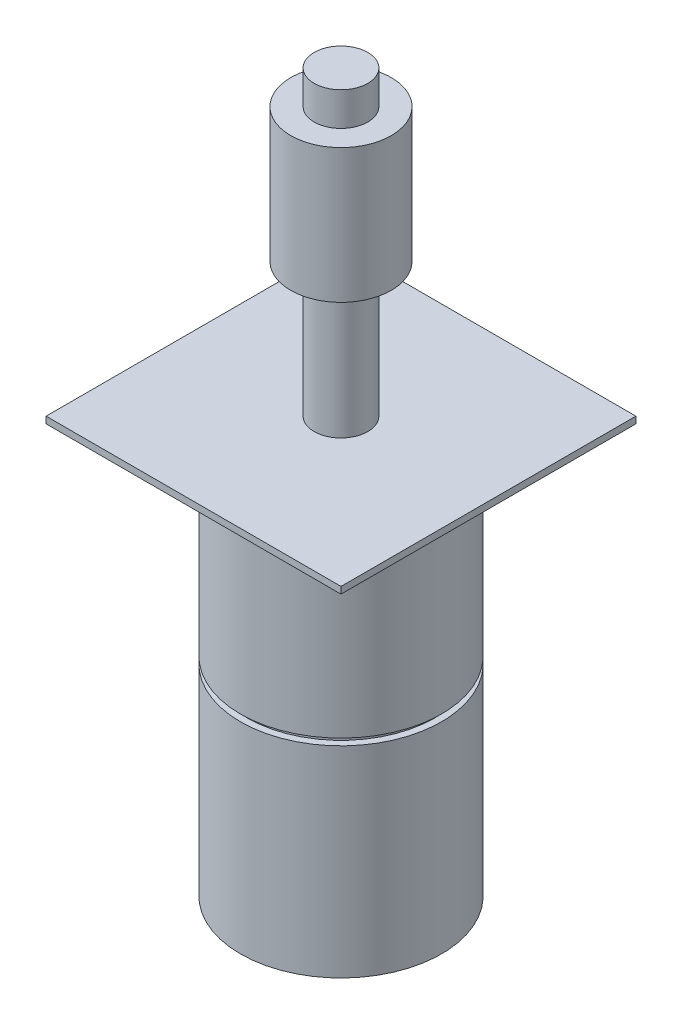
SolidWorks part; units mm, degrees
ref_plane "Front Plane" through (0, 0, 0) normal (0, 0, 1) x (1, 0, 0)
ref_plane "Top Plane" through (0, 0, 0) normal (0, 1, 0) x (1, 0, 0)
ref_plane "Right Plane" through (0, 0, 0) normal (1, 0, 0) x (0, 0, -1)
sketch "Sketch1" plane through (0, 0, 0) normal (0, 1, 0) x (1, 0, 0)
  circle A0 centre (0, 0) radius 15
extrude "Boss-Extrude1" add sketch "Sketch1" along normal blind 30
ref_plane "Plane1" through (0, 30, 0) normal (0, 1, 0) x (1, 0, 0)
sketch "Sketch2" plane through (0, 30, 0) normal (0, 1, 0) x (1, 0, 0)
  line L1 (-22, 22) -> (22, 22)
  line L2 (-22, 22) -> (-22, -22)
  line L3 (-22, -22) -> (22, -22)
  line L4 (22, 22) -> (22, -22)
  line L5 (-22, 22) -> (22, -22) construction
  line L6 (-22, -22) -> (22, 22) construction
  point P0 (0, 0)
  dimension "D1" = 44
  dimension "D2" = 44
extrude "Boss-Extrude2" add sketch "Sketch2" along normal blind 1
ref_plane "Plane2" through (0, 31, 0) normal (0, 1, 0) x (1, 0, 0)
sketch "Sketch3" plane through (0, 31, 0) normal (0, 1, 0) x (1, 0, 0)
  circle A0 centre (0, 0) radius 4
extrude "Boss-Extrude3" add sketch "Sketch3" along normal blind 20
ref_plane "Plane3" through (0, 51, 0) normal (0, 1, 0) x (1, 0, 0)
sketch "Sketch4" plane through (0, 51, 0) normal (0, 1, 0) x (1, 0, 0)
  circle A0 centre (0, 0) radius 7.5
extrude "Boss-Extrude4" add sketch "Sketch4" along normal blind 20
ref_plane "Plane4" through (0, 71, 0) normal (0, 1, 0) x (1, 0, 0)
sketch "Sketch5" plane through (0, 71, 0) normal (0, 1, 0) x (1, 0, 0)
  circle A0 centre (0, 0) radius 4
extrude "Boss-Extrude5" add sketch "Sketch5" along normal blind 5
ref_plane "Plane5" through (0, 0, 0) normal (0, -1, 0) x (-1, 0, 0)
sketch "Sketch6" plane through (0, 0, 0) normal (0, -1, 0) x (-1, 0, 0)
  circle A0 centre (0, 0) radius 14
extrude "Boss-Extrude6" add sketch "Sketch6" along normal blind 1
ref_plane "Plane6" through (0, -1, 0) normal (0, -1, 0) x (-1, 0, 0)
sketch "Sketch7" plane through (0, -1, 0) normal (0, -1, 0) x (-1, 0, 0)
  circle A0 centre (0, 0) radius 15
extrude "Boss-Extrude7" add sketch "Sketch7" along normal blind 30
ref_plane "Plane7" through (0, -31, 0) normal (0, -1, 0) x (-1, 0, 0)
sketch "Sketch8" plane through (0, -31, 0) normal (0, -1, 0) x (-1, 0, 0)
  circle A0 centre (0, 0) radius 4
extrude "Boss-Extrude8" add sketch "Sketch8" along normal blind 5
